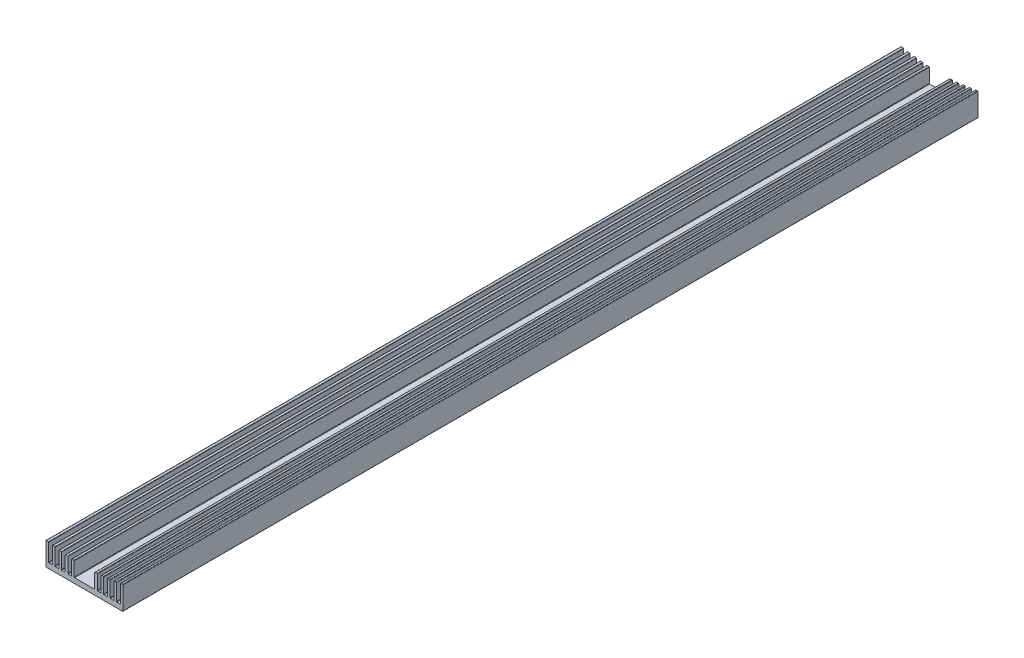
SolidWorks part; units mm, degrees
material "6063-T6"
ref_plane "Спереди" through (0, 0, 0) normal (0, 0, 1) x (1, 0, 0)
ref_plane "Сверху" through (0, 0, 0) normal (0, 1, 0) x (1, 0, 0)
ref_plane "Справа" through (0, 0, 0) normal (1, 0, 0) x (0, 0, -1)
sketch "Model" plane through (0, 0, 0) normal (0, 0, 1) x (1, 0, 0)
  line L46 (-45, 0.5) -> (-45, 26.8946)
  line L47 (-44.4022, 27.385) -> (-42.4066, 26.9962)
  line L48 (-42, 26.505) -> (-42, 6.5)
  line L49 (-41.5, 6) -> (-38, 6)
  line L50 (-37.5, 6.5) -> (-37.5, 25.529)
  line L51 (-36.9187, 26.0223) -> (-34.9231, 25.7025)
  line L52 (-34.5, 25.2084) -> (-34.5, 6.5)
  line L53 (-34, 6) -> (-30.5, 6)
  line L54 (-30, 6.5) -> (-30, 24.4207)
  line L55 (-29.4352, 24.9165) -> (-27.4396, 24.6645)
  line L56 (-27, 24.1682) -> (-27, 6.5)
  line L57 (-26.5, 6) -> (-23, 6)
  line L58 (-22.5, 6.5) -> (-22.5, 23.5662)
  line L59 (-21.9516, 24.0639) -> (-19.956, 23.8789)
  line L60 (-19.5, 23.3808) -> (-19.5, 6.5)
  line L61 (-19, 6) -> (-15.5, 6)
  line L62 (-15, 6.5) -> (-15, 22.9626)
  line L63 (-14.4681, 23.4615) -> (-12.4725, 23.3429)
  line L64 (-12, 22.8437) -> (-12, 6.5)
  line L65 (-11.5, 6) -> (11.5, 6)
  line L66 (12, 6.5) -> (12, 22.8437)
  line L67 (12.4725, 23.3429) -> (14.4681, 23.4615)
  line L68 (15, 22.9626) -> (15, 6.5)
  line L69 (15.5, 6) -> (19, 6)
  line L70 (19.5, 6.5) -> (19.5, 23.3808)
  line L71 (19.956, 23.8789) -> (21.9516, 24.0639)
  line L72 (22.5, 23.5662) -> (22.5, 6.5)
  line L73 (23, 6) -> (26.5, 6)
  line L74 (27, 6.5) -> (27, 24.1682)
  line L75 (27.4396, 24.6645) -> (29.4352, 24.9165)
  line L76 (30, 24.4207) -> (30, 6.5)
  line L77 (30.5, 6) -> (34, 6)
  line L78 (34.5, 6.5) -> (34.5, 25.2084)
  line L79 (34.9231, 25.7025) -> (36.9187, 26.0223)
  line L80 (37.5, 25.529) -> (37.5, 6.5)
  line L81 (38, 6) -> (41.5, 6)
  line L82 (42, 6.5) -> (42, 26.505)
  line L83 (42.4066, 26.9962) -> (44.4022, 27.385)
  line L84 (45, 26.8946) -> (45, 0.5)
  line L85 (44.5, 0) -> (-44.5, 0)
  arc A41 (-44.4022, 27.385) -> (-45, 26.8946) centre (-44.5, 26.8946) ccw
  arc A42 (-42, 26.505) -> (-42.4066, 26.9962) centre (-42.5, 26.505) ccw
  arc A43 (-42, 6.5) -> (-41.5, 6) centre (-41.5, 6.5) ccw
  arc A44 (-38, 6) -> (-37.5, 6.5) centre (-38, 6.5) ccw
  arc A45 (-36.9187, 26.0223) -> (-37.5, 25.529) centre (-37, 25.529) ccw
  arc A46 (-34.5, 25.2084) -> (-34.9231, 25.7025) centre (-35, 25.2084) ccw
  arc A47 (-34.5, 6.5) -> (-34, 6) centre (-34, 6.5) ccw
  arc A48 (-30.5, 6) -> (-30, 6.5) centre (-30.5, 6.5) ccw
  arc A49 (-29.4352, 24.9165) -> (-30, 24.4207) centre (-29.5, 24.4207) ccw
  arc A50 (-27, 24.1682) -> (-27.4396, 24.6645) centre (-27.5, 24.1682) ccw
  arc A51 (-27, 6.5) -> (-26.5, 6) centre (-26.5, 6.5) ccw
  arc A52 (-23, 6) -> (-22.5, 6.5) centre (-23, 6.5) ccw
  arc A53 (-21.9516, 24.0639) -> (-22.5, 23.5662) centre (-22, 23.5662) ccw
  arc A54 (-19.5, 23.3808) -> (-19.956, 23.8789) centre (-20, 23.3808) ccw
  arc A55 (-19.5, 6.5) -> (-19, 6) centre (-19, 6.5) ccw
  arc A56 (-15.5, 6) -> (-15, 6.5) centre (-15.5, 6.5) ccw
  arc A57 (-14.4681, 23.4615) -> (-15, 22.9626) centre (-14.5, 22.9626) ccw
  arc A58 (-12, 22.8437) -> (-12.4725, 23.3429) centre (-12.5, 22.8437) ccw
  arc A59 (-12, 6.5) -> (-11.5, 6) centre (-11.5, 6.5) ccw
  arc A60 (11.5, 6) -> (12, 6.5) centre (11.5, 6.5) ccw
  arc A61 (12.4725, 23.3429) -> (12, 22.8437) centre (12.5, 22.8437) ccw
  arc A62 (15, 22.9626) -> (14.4681, 23.4615) centre (14.5, 22.9626) ccw
  arc A63 (15, 6.5) -> (15.5, 6) centre (15.5, 6.5) ccw
  arc A64 (19, 6) -> (19.5, 6.5) centre (19, 6.5) ccw
  arc A65 (19.956, 23.8789) -> (19.5, 23.3808) centre (20, 23.3808) ccw
  arc A66 (22.5, 23.5662) -> (21.9516, 24.0639) centre (22, 23.5662) ccw
  arc A67 (22.5, 6.5) -> (23, 6) centre (23, 6.5) ccw
  arc A68 (26.5, 6) -> (27, 6.5) centre (26.5, 6.5) ccw
  arc A69 (27.4396, 24.6645) -> (27, 24.1682) centre (27.5, 24.1682) ccw
  arc A70 (30, 24.4207) -> (29.4352, 24.9165) centre (29.5, 24.4207) ccw
  arc A71 (30, 6.5) -> (30.5, 6) centre (30.5, 6.5) ccw
  arc A72 (34, 6) -> (34.5, 6.5) centre (34, 6.5) ccw
  arc A73 (34.9231, 25.7025) -> (34.5, 25.2084) centre (35, 25.2084) ccw
  arc A74 (37.5, 25.529) -> (36.9187, 26.0223) centre (37, 25.529) ccw
  arc A75 (37.5, 6.5) -> (38, 6) centre (38, 6.5) ccw
  arc A76 (41.5, 6) -> (42, 6.5) centre (41.5, 6.5) ccw
  arc A77 (42.4066, 26.9962) -> (42, 26.505) centre (42.5, 26.505) ccw
  arc A78 (45, 26.8946) -> (44.4022, 27.385) centre (44.5, 26.8946) ccw
  arc A79 (44.5, 0) -> (45, 0.5) centre (44.5, 0.5) ccw
  arc A80 (-45, 0.5) -> (-44.5, 0) centre (-44.5, 0.5) ccw
extrude "Бобышка-Вытянуть1" add sketch "Model" along normal blind 1000 contours L46 A80 L85 A79 L84 A78 L83 A77 L82 A76 L81 A75 L80 A74 L79 A73 L78 A72 L77 A71 L76 A70 L75 A69 L74 A68 L73 A67 L72 A66 L71 A65 L70 A64 L69 A63 L68 A62 L67 A61 L66 A60 L65 A59 L64 A58 L63 A57 L62 A56 L61
